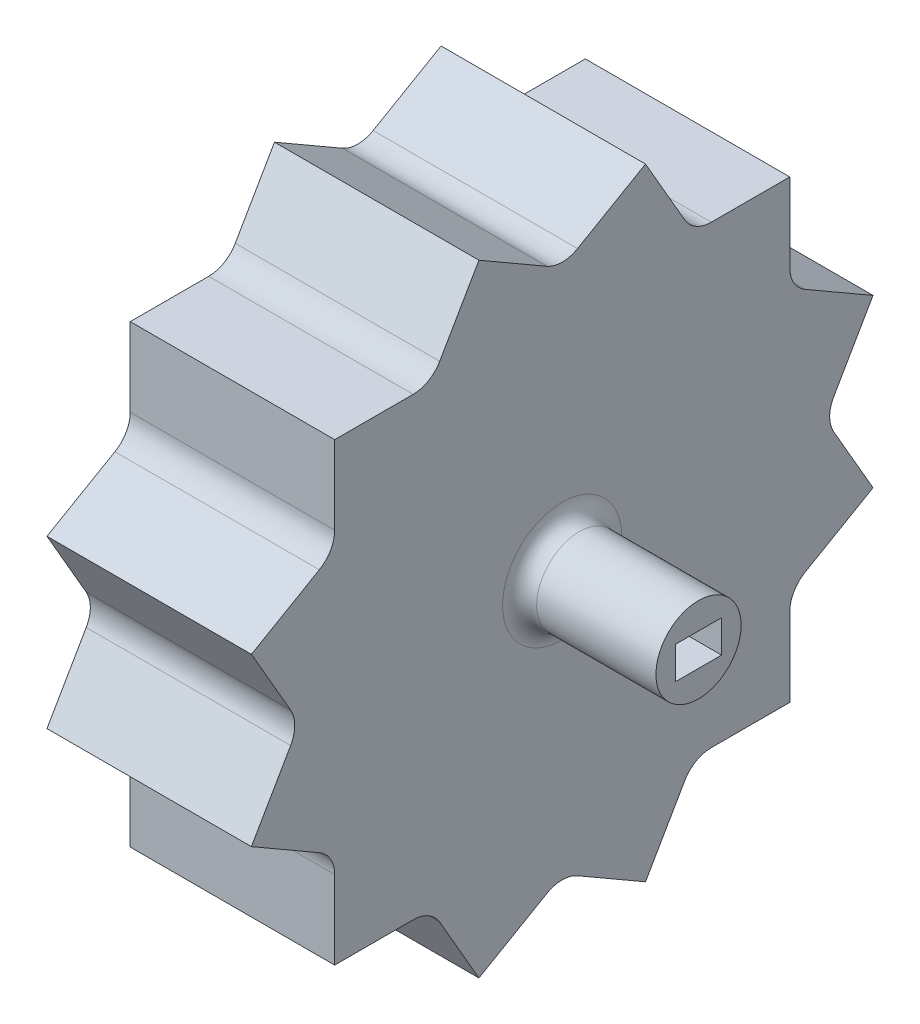
SolidWorks part; units mm, degrees
ref_plane "Front Plane" through (0, 0, 0) normal (0, 0, 1) x (1, 0, 0)
ref_plane "Top Plane" through (0, 0, 0) normal (0, 1, 0) x (1, 0, 0)
ref_plane "Right Plane" through (0, 0, 0) normal (1, 0, 0) x (0, 0, -1)
sketch "Sketch1" plane through (0, 0, 0) normal (1, 0, 0) x (0, 0, -1)
  line L0 (1.8, 31.8823) -> (9.7769, 36.4878)
  line L1 (9.7769, 36.4878) -> (14.3823, 28.5109)
  line L2 (17.5, 26.7109) -> (26.7109, 26.7109)
  line L3 (26.7109, 26.7109) -> (26.7109, 17.5)
  line L4 (28.5109, 14.3823) -> (36.4878, 9.7769)
  line L5 (36.4878, 9.7769) -> (31.8823, 1.8)
  line L6 (31.8823, -1.8) -> (36.4878, -9.7769)
  line L7 (36.4878, -9.7769) -> (28.5109, -14.3823)
  line L8 (26.7109, -17.5) -> (26.7109, -26.7109)
  line L9 (26.7109, -26.7109) -> (17.5, -26.7109)
  line L10 (14.3823, -28.5109) -> (9.7769, -36.4878)
  line L11 (9.7769, -36.4878) -> (1.8, -31.8823)
  line L12 (-1.8, -31.8823) -> (-9.7769, -36.4878)
  line L13 (-9.7769, -36.4878) -> (-14.3823, -28.5109)
  line L14 (-17.5, -26.7109) -> (-26.7109, -26.7109)
  line L15 (-26.7109, -26.7109) -> (-26.7109, -17.5)
  line L16 (-28.5109, -14.3823) -> (-36.4878, -9.7769)
  line L17 (-36.4878, -9.7769) -> (-31.8823, -1.8)
  line L18 (-31.8823, 1.8) -> (-36.4878, 9.7769)
  line L19 (-36.4878, 9.7769) -> (-28.5109, 14.3823)
  line L20 (-26.7109, 17.5) -> (-26.7109, 26.7109)
  line L21 (-26.7109, 26.7109) -> (-17.5, 26.7109)
  line L22 (-14.3823, 28.5109) -> (-9.7769, 36.4878)
  line L23 (-9.7769, 36.4878) -> (-1.8, 31.8823)
  line L24 (0, 0) -> (0, 112.2055) construction
  line L25 (0, 0) -> (9.7769, 36.4878) construction
  line L26 (-24.2294, 45.5997) -> (43.7832, 27.3758) construction
  line L27 (-11.5161, 39.3204) -> (47.9644, 23.3827) construction
  circle A0 centre (0, 0) radius 35 construction
  arc A1 (-1.8, 31.8823) -> (1.8, 31.8823) centre (0, 35) ccw
  arc A2 (14.3823, 28.5109) -> (17.5, 26.7109) centre (17.5, 30.3109) ccw
  arc A3 (26.7109, 17.5) -> (28.5109, 14.3823) centre (30.3109, 17.5) ccw
  arc A4 (31.8823, 1.8) -> (31.8823, -1.8) centre (35, 0) ccw
  arc A5 (28.5109, -14.3823) -> (26.7109, -17.5) centre (30.3109, -17.5) ccw
  arc A6 (17.5, -26.7109) -> (14.3823, -28.5109) centre (17.5, -30.3109) ccw
  arc A7 (1.8, -31.8823) -> (-1.8, -31.8823) centre (0, -35) ccw
  arc A8 (-14.3823, -28.5109) -> (-17.5, -26.7109) centre (-17.5, -30.3109) ccw
  arc A9 (-26.7109, -17.5) -> (-28.5109, -14.3823) centre (-30.3109, -17.5) ccw
  arc A10 (-31.8823, -1.8) -> (-31.8823, 1.8) centre (-35, 0) ccw
  arc A11 (-28.5109, 14.3823) -> (-26.7109, 17.5) centre (-30.3109, 17.5) ccw
  arc A12 (-17.5, 26.7109) -> (-14.3823, 28.5109) centre (-17.5, 30.3109) ccw
  point P16 (9.7769, 36.4878)
  point P65 (0, 0)
  dimension "D1" = 70
  dimension "D2" = 3.6
  dimension "D4" = 60
  dimension "D3" = 12
extrude "Boss-Extrude1" add sketch "Sketch1" along normal blind 24
sketch "Sketch2" plane through (24, 0, 0) normal (1, 0, 0) x (0, 0, -1)
  circle A0 centre (0, 0) radius 5
  dimension "D1" = 10
extrude "Boss-Extrude2" add sketch "Sketch2" along normal blind 16
fillet "Fillet1" radius 2 1 edges at (24, 0, -5)
sketch "Sketch4" plane through (40, 0, 0) normal (1, 0, 0) x (0, 0, -1)
  line L1 (-2.705, -1.9) -> (2.705, -1.9)
  line L2 (-2.705, -1.9) -> (-2.705, 1.9)
  line L3 (-2.705, 1.9) -> (2.705, 1.9)
  line L4 (2.705, -1.9) -> (2.705, 1.9)
  line L5 (-2.705, -1.9) -> (2.705, 1.9) construction
  line L6 (-2.705, 1.9) -> (2.705, -1.9) construction
  point P0 (0, 0)
  dimension "D1" = 5.41
  dimension "D2" = 3.8
extrude "Cut-Extrude1" cut sketch "Sketch4" against normal blind 20
